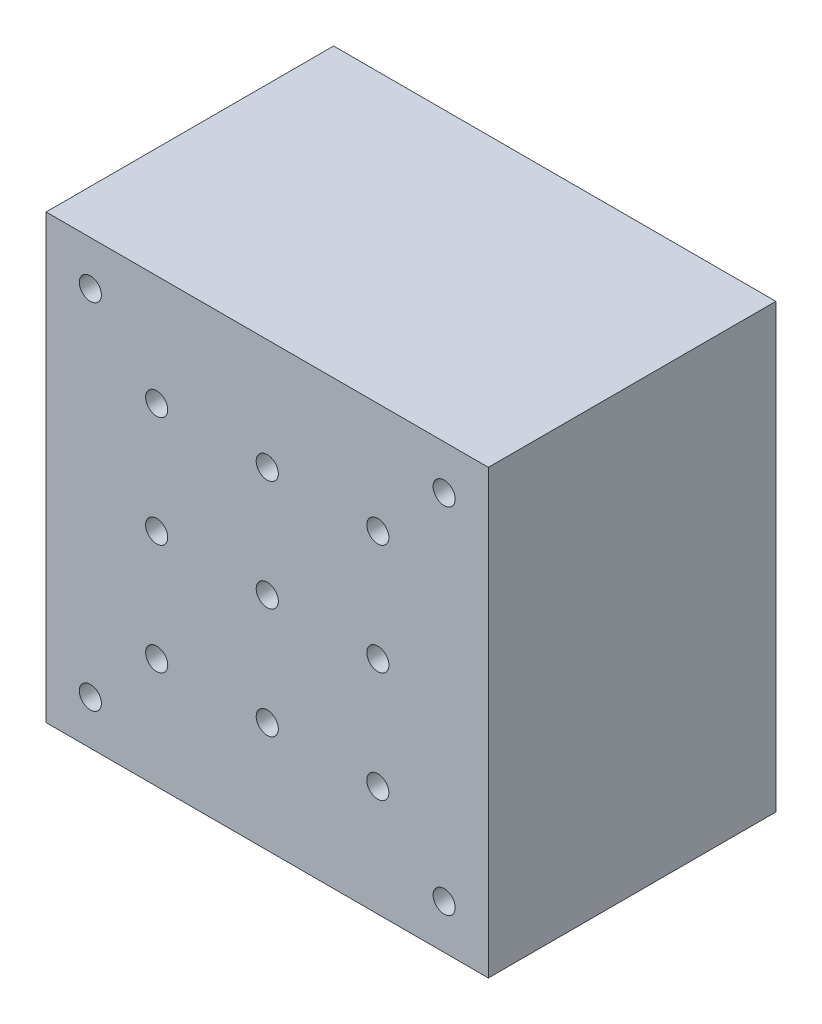
SolidWorks part; units mm, degrees
ref_plane "Front Plane" through (0, 0, 0) normal (0, 0, 1) x (1, 0, 0)
ref_plane "Top Plane" through (0, 0, 0) normal (0, 1, 0) x (1, 0, 0)
ref_plane "Right Plane" through (0, 0, 0) normal (1, 0, 0) x (0, 0, -1)
sketch "Sketch1" plane through (0, 0, 0) normal (0, 0, 1) x (1, 0, 0)
  line L1 (-63.5, -63.5) -> (63.5, -63.5)
  line L2 (-63.5, -63.5) -> (-63.5, 63.5)
  line L3 (-63.5, 63.5) -> (63.5, 63.5)
  line L4 (63.5, -63.5) -> (63.5, 63.5)
  line L5 (-63.5, -63.5) -> (63.5, 63.5) construction
  line L6 (-63.5, 63.5) -> (63.5, -63.5) construction
  point P0 (0, 0)
  dimension "D1" = 127
  dimension "D2" = 127
extrude "Boss-Extrude1" add sketch "Sketch1" along normal blind 82.55
sketch "Sketch2" plane through (0, 0, 82.55) normal (0, 0, 1) x (1, 0, 0)
  circle A0 centre (0, 0) radius 3.175
  dimension "D1" = 6.35
extrude "Cut-Extrude1" cut sketch "Sketch2" against normal through all
pattern_linear "LPattern1" count 2 spacing 31.75 along (-1, 0, 0) count 2 spacing 31.75 along (1, 0, 0) of "Cut-Extrude1"
pattern_linear "LPattern2" count 2 spacing 31.75 along (0, -1, 0) count 2 spacing 31.75 along (0, 1, 0) of "LPattern1", "Cut-Extrude1"
sketch "Sketch3" plane through (0, 0, 82.55) normal (0, 0, 1) x (1, 0, 0)
  circle A0 centre (-50.8, 50.8) radius 3.175
  circle A1 centre (50.8, 50.8) radius 3.175
  circle A2 centre (50.8, -50.8) radius 3.175
  circle A3 centre (-50.8, -50.8) radius 3.175
  dimension "D1" = 6.35
  dimension "D2" = 50.8
  dimension "D3" = 50.8
  dimension "D4" = 50.8
  dimension "D5" = 50.8
extrude "Cut-Extrude2" cut sketch "Sketch3" against normal through all
